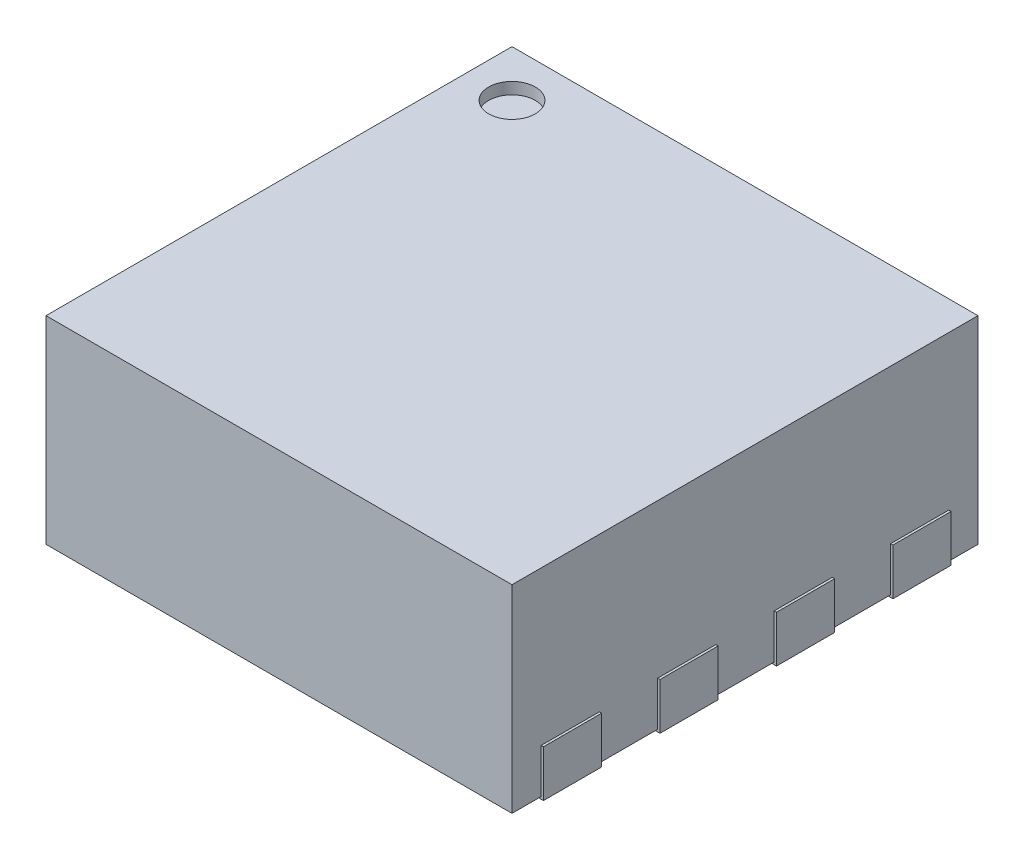
SolidWorks part; units mm, degrees
ref_plane "Front Plane" through (0, 0, 0) normal (0, 0, 1) x (1, 0, 0)
ref_plane "Top Plane" through (0, 0, 0) normal (0, 1, 0) x (1, 0, 0)
ref_plane "Right Plane" through (0, 0, 0) normal (1, 0, 0) x (0, 0, -1)
sketch "Sketch1" plane through (0, 0, 0) normal (0, 1, 0) x (1, 0, 0)
  line L1 (-1, -1) -> (1, -1)
  line L2 (-1, -1) -> (-1, 1)
  line L3 (-1, 1) -> (1, 1)
  line L4 (1, -1) -> (1, 1)
  line L5 (-1, -1) -> (1, 1) construction
  line L6 (-1, 1) -> (1, -1) construction
  point P0 (0, 0)
  dimension "D1" = 2
  dimension "D2" = 2
extrude "Boss-Extrude1" add sketch "Sketch1" along normal blind 0.85
sketch "Sketch2" plane through (0, 0, 0) normal (0, 1, 0) x (1, 0, 0)
  line L0 (-1, 1) -> (-1, -1) construction
  line L1 (-1.01, 0.375) -> (-0.71, 0.375)
  line L2 (-1.01, 0.375) -> (-1.01, 0.125)
  line L3 (-1.01, 0.125) -> (-0.71, 0.125)
  line L4 (-0.71, 0.375) -> (-0.71, 0.125)
  line L5 (0, 1) -> (0, -1) construction
  line L6 (1, 1) -> (-1, 1) construction
  line L7 (-1, -1) -> (1, -1) construction
  line L8 (-1.01, 0.875) -> (-1.01, 0.625)
  line L9 (-1.01, 0.875) -> (-0.71, 0.875)
  line L10 (-0.71, 0.875) -> (-0.71, 0.625)
  line L11 (-1.01, 0.625) -> (-0.71, 0.625)
  line L12 (-1.01, -0.125) -> (-1.01, -0.375)
  line L13 (-1.01, -0.125) -> (-0.71, -0.125)
  line L14 (-0.71, -0.125) -> (-0.71, -0.375)
  line L15 (-1.01, -0.375) -> (-0.71, -0.375)
  line L16 (-1.01, -0.625) -> (-1.01, -0.875)
  line L17 (-1.01, -0.625) -> (-0.71, -0.625)
  line L18 (-0.71, -0.625) -> (-0.71, -0.875)
  line L19 (-1.01, -0.875) -> (-0.71, -0.875)
  line L20 (1.01, -0.875) -> (0.71, -0.875)
  line L21 (0.71, -0.625) -> (0.71, -0.875)
  line L22 (1.01, -0.625) -> (0.71, -0.625)
  line L23 (1.01, -0.625) -> (1.01, -0.875)
  line L24 (1.01, -0.375) -> (0.71, -0.375)
  line L25 (0.71, -0.125) -> (0.71, -0.375)
  line L26 (1.01, -0.125) -> (0.71, -0.125)
  line L27 (1.01, -0.125) -> (1.01, -0.375)
  line L28 (1.01, 0.625) -> (0.71, 0.625)
  line L29 (0.71, 0.875) -> (0.71, 0.625)
  line L30 (1.01, 0.875) -> (0.71, 0.875)
  line L31 (1.01, 0.875) -> (1.01, 0.625)
  line L32 (0.71, 0.375) -> (0.71, 0.125)
  line L33 (1.01, 0.125) -> (0.71, 0.125)
  line L34 (1.01, 0.375) -> (1.01, 0.125)
  line L35 (1.01, 0.375) -> (0.71, 0.375)
  dimension "D1" = 0.01
  dimension "D2" = 0.25
  dimension "D3" = 0.125
  dimension "D4" = 0.3
  dimension "D6" = 0.5
  dimension "D8" = 0.5
  dimension "D5" = 2
  dimension "D7" = 3
extrude "Boss-Extrude2" add sketch "Sketch2" along normal blind 0.2 from offset 0.01 separate body offset against normal yes
sketch "Sketch3" plane through (0, 0.85, 0) normal (0, 1, 0) x (1, 0, 0)
  line L0 (1, 1) -> (-1, 1) construction
  line L1 (-1, 1) -> (-1, -1) construction
  circle A0 centre (-0.8, 0.8) radius 0.1
  dimension "D1" = 0.2
  dimension "D2" = 0.2
  dimension "D3" = 0.2
extrude "Cut-Extrude1" cut sketch "Sketch3" against normal blind 0.05
